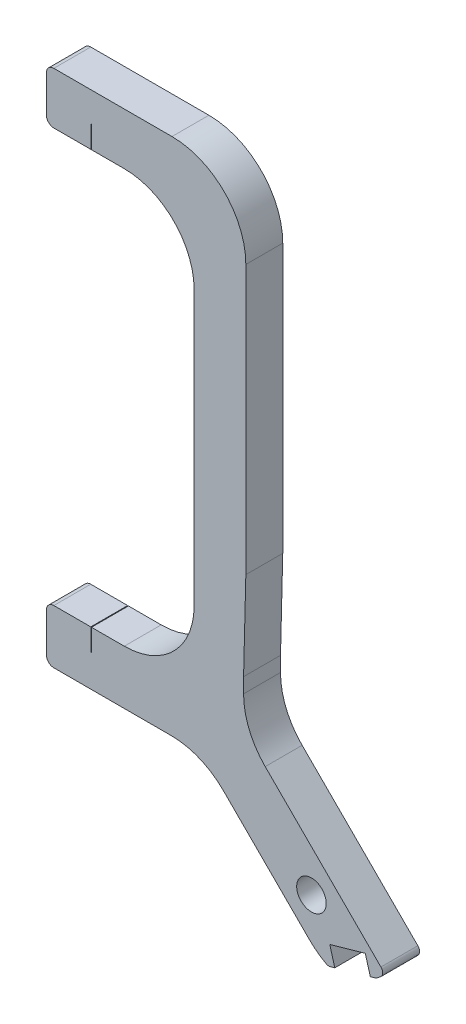
SolidWorks part; units mm, degrees
ref_plane "Front Plane" through (0, 0, 0) normal (0, 0, 1) x (1, 0, 0)
ref_plane "Top Plane" through (0, 0, 0) normal (0, 1, 0) x (1, 0, 0)
ref_plane "Right Plane" through (0, 0, 0) normal (1, 0, 0) x (0, 0, -1)
sketch "Sketch1" plane through (0, 0, 0) normal (0, 0, 1) x (1, 0, 0)
  line L0 (1, 0) -> (17, 0)
  line L1 (27, -10.1647) -> (27, -46.3772)
  line L2 (16.8019, -70.3054) -> (1, -70.3054)
  line L3 (0, -69.3054) -> (0, -64)
  line L4 (1, -63) -> (10.5397, -63)
  line L5 (20, -53.5397) -> (20, -16.4603)
  line L6 (10.5397, -7) -> (1, -7)
  line L7 (0, -6) -> (0, -1)
  line L14 (27, -10.1647) -> (27, -10)
  line L34 (16.8019, -70.3054) -> (26.6946, -70.3054) construction
  line L37 (26.6946, -58.4939) -> (27, -46.3772)
  line L42 (26.6946, -70.3054) -> (26.6946, -58.4939) construction
  line L43 (26.6946, -70.3054) -> (41.8593, -85.47) construction
  line L45 (35.5979, -84.8655) -> (21.0378, -70.3054)
  line L48 (45.2918, -83.2457) -> (26.6946, -64.6485)
  line L49 (37.7477, -85.47) -> (26.6946, -68.5482) construction
  line L50 (24.9375, -70.3054) -> (37.6921, -78.6364) construction
  line L53 (16.8019, -70.3054) -> (21.0378, -70.3054)
  line L54 (26.6946, -58.4939) -> (26.6946, -64.3996)
  line L55 (26.6946, -64.3996) -> (26.6946, -64.6485)
  line L58 (43.4863, -87.0971) -> (46.4915, -90.1022) construction
  line L59 (45.2054, -84.4519) -> (44.7499, -84.7928)
  line L63 (40.9545, -84.5652) -> (41.8968, -84.2994) construction
  line L64 (44.4887, -84.9219) -> (38.462, -86.63)
  arc A2 (10.5397, -63) -> (20, -53.5397) centre (10.5397, -53.5397) ccw
  arc A3 (20, -16.4603) -> (10.5397, -7) centre (10.5397, -16.4603) ccw
  arc A4 (0, -64) -> (1, -63) centre (1, -64) cw
  arc A5 (0, -69.3054) -> (1, -70.3054) centre (1, -69.3054) ccw
  arc A6 (0, -1) -> (1, 0) centre (1, -1) cw
  arc A7 (0, -6) -> (1, -7) centre (1, -6) ccw
  arc A8 (17, 0) -> (27, -10) centre (17, -10) cw
  circle A10 centre (35.887, -79.4977) radius 2
  arc A14 (37.8591, -86.5617) -> (35.5979, -84.8655) centre (42.669, -77.7944) cw
  arc A17 (44.7499, -84.7928) -> (44.4887, -84.9219) centre (44.2706, -84.1522) cw
  arc A18 (45.2918, -83.2457) -> (45.2054, -84.4519) centre (44.7261, -83.8114) cw
  arc A19 (37.8591, -86.5617) -> (38.462, -86.63) centre (38.2439, -85.8603) ccw
  point P11 (27, 0)
  point P25 (0, 0)
  point P30 (37.4955, 3.7564)
  point P31 (30.004, -73.6147)
  point P56 (38.0464, -86.3113)
  point P57 (44.4887, -84.9219)
  dimension "D8" = 1
  dimension "D6" = 10
  dimension "D7" = 4
  dimension "D10" = 10
  dimension "D9" = 0.8
  dimension "D11" = 0.8
  dimension "D1" = 7
  dimension "D2" = 7
  dimension "D4" = 20
  dimension "D3" = 135
  dimension "D5" = 13
  dimension "D12" = 15.823
extrude "Boss-Extrude1" add sketch "Sketch1" along normal blind 5
sketch "Sketch2" plane through (0, -63, 0) normal (0, 1, 0) x (1, 0, 0)
  line L0 (27, -2.5) -> (6.05, -2.5) construction
  line L1 (27, -5) -> (27, 0) construction
  line L2 (10.5397, 0) -> (1, 0) construction
  line L3 (6, -5) -> (6.1, -5)
  line L4 (6, -5) -> (6, 0)
  line L5 (6, 0) -> (6.1, 0)
  line L6 (6.1, -5) -> (6.1, 0)
  line L7 (6, -5) -> (6.1, 0) construction
  line L8 (6, 0) -> (6.1, -5) construction
  dimension "D2" = 0.1
extrude "Cut-Extrude1" cut sketch "Sketch2" against normal blind 3
sketch "Sketch3" plane through (0, -7, 0) normal (0, -1, 0) x (1, 0, 0)
  line L0 (27, 2.5) -> (6.05, 2.5) construction
  line L1 (27, 5) -> (27, 0) construction
  line L2 (1, 5) -> (10.5397, 5) construction
  line L3 (6, 0) -> (6.1, 0)
  line L4 (6, 0) -> (6, 5)
  line L5 (6, 5) -> (6.1, 5)
  line L6 (6.1, 0) -> (6.1, 5)
  line L7 (6, 0) -> (6.1, 5) construction
  line L8 (6, 5) -> (6.1, 0) construction
  dimension "D2" = 0.1
extrude "Cut-Extrude2" cut sketch "Sketch3" against normal blind 3
sketch "Sketch4" plane through (25.5862, -90.2791, 0) normal (0.2727, -0.9621, 0) x (0.9621, 0.2727, 0)
  line L0 (13.3829, 5) -> (19.647, 5) construction
  line L1 (18.9907, 5) -> (13.9907, 5)
  line L2 (18.9907, 5) -> (18.9907, 0)
  line L3 (18.9907, 0) -> (13.9907, 0)
  line L4 (13.9907, 5) -> (13.9907, 0)
  line L5 (13.3829, 0) -> (19.647, 0) construction
  dimension "D1" = 5
extrude "Cut-Extrude3" cut sketch "Sketch4" against normal blind 2.5
fillet "Fillet1" radius 10 2 edges at (21.0378, -70.3054, 2.5) (26.6946, -64.6485, 2.5)
equation "\"A.L\"= 0.07m"
equation "\"A.h\"= 0.007m"
equation "\"A.d\"= 0.005m"
equation "\"A.delta\"= 45.0001"
equation "\"A.w\"= 0m"
equation "\"A.v\"= 0.013m"
equation "\"A.s\"= 0.014m"
equation "\"A.t\"= 0.007m"
equation "\"B.L\"= 0.065m"
equation "\"B.h\"= 0.008m"
equation "\"B.s\"= 0.016m"
equation "\"B.t\"= 0.008m"
equation "\"C.h\"= 0.0065m"
equation "\"C.d\"= 0.005m"
equation "\"C.L\"= 0.05m"
equation "\"C.wmax\"= 0.003m"
equation "\"D.L\"= 0.06m"
equation "\"D.h\"= 0.008m"
equation "\"D.s\"= 0.012m"
equation "\"D.t\"= 0.008m"
equation "\"a_h\"= 0.0001m"
equation "\"a_d\"= 0.005m"
equation "\"a_L\"= 0.008m"
equation "\"b_h\"= 0.0004m"
equation "\"b_d\"= 0.005m"
equation "\"b_L\"= 0.008m"
equation "\"c_h\"= 0.0001m"
equation "\"c_d\"= 0.005m"
equation "\"c_L\"= 0.01m"
equation "\"d_h\"= 0.0001m"
equation "\"d_d\"= 0.005m"
equation "\"d_L\"= 0.01m"
equation "\"S.h\"= 0.015m"
equation "\"S.L\"= 0.09175m"
equation "\"D1@Sketch1\"=\"A.h\""
equation "\"D2@Sketch1\"=\"A.t\""
equation "\"D4@Sketch1\"=\"A.s\"+0.006"
equation "\"D1@Boss-Extrude1\"=\"A.d\""
equation "\"D1@Sketch2\"=\"A.h\"+\"A.s\"-\"a_h\"/2"
equation "\"D2@Sketch2\"=\"d_h\""
equation "\"D1@Sketch3\"=\"A.h\"+\"A.s\"-\"d_h\"/2"
equation "\"D2@Sketch3\"=\"d_h\""
equation "\"D5@Sketch1\"=0.013m"
